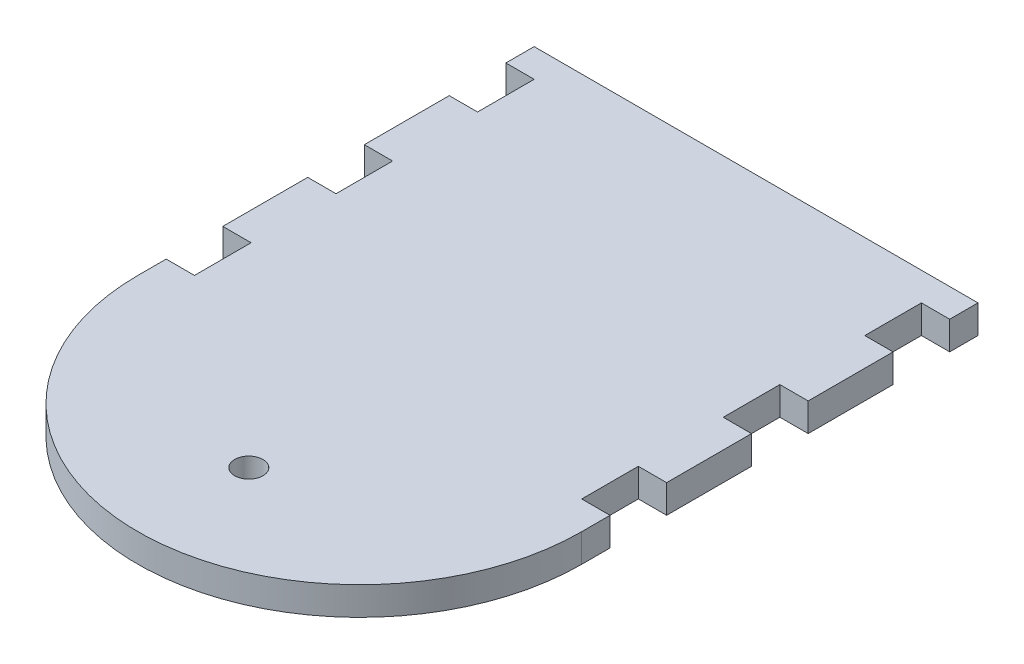
SolidWorks part; units mm, degrees
ref_plane "Front Plane" through (0, 0, 0) normal (0, 0, 1) x (1, 0, 0)
ref_plane "Top Plane" through (0, 0, 0) normal (0, 1, 0) x (1, 0, 0)
ref_plane "Right Plane" through (0, 0, 0) normal (1, 0, 0) x (0, 0, -1)
sketch "Sketch1" plane through (0, 0, 0) normal (0, 1, 0) x (1, 0, 0)
  line L0 (-49.784, 0) -> (49.784, 0) construction
  line L1 (-49.784, 44.45) -> (49.784, 44.45) construction
  line L2 (-49.784, 44.45) -> (-49.784, -44.45) construction
  line L3 (-49.784, -44.45) -> (49.784, -44.45) construction
  line L4 (49.784, 44.45) -> (49.784, -44.45) construction
  line L5 (-49.784, 44.45) -> (49.784, -44.45) construction
  line L6 (-49.784, -44.45) -> (49.784, 44.45) construction
  line L7 (-49.784, 44.45) -> (49.784, 44.45)
  line L8 (49.784, 44.45) -> (49.784, 38.1)
  line L9 (49.784, 38.1) -> (43.434, 38.1)
  line L10 (43.434, 38.1) -> (43.434, 25.4)
  line L11 (43.434, 25.4) -> (49.784, 25.4)
  line L12 (49.784, 25.4) -> (49.784, 6.35)
  line L13 (49.784, 6.35) -> (43.434, 6.35)
  line L14 (43.434, 6.35) -> (43.434, -6.35)
  line L15 (43.434, -6.35) -> (49.784, -6.35)
  line L16 (49.784, -6.35) -> (49.784, -25.4)
  line L17 (49.784, -25.4) -> (43.434, -25.4)
  line L18 (43.434, -25.4) -> (43.434, -38.1)
  line L19 (43.434, -38.1) -> (49.784, -38.1)
  line L20 (49.784, -38.1) -> (49.784, -44.45)
  line L21 (0, 44.45) -> (0, -44.45) construction
  line L22 (-43.434, -38.1) -> (-49.784, -38.1)
  line L23 (-43.434, -25.4) -> (-43.434, -38.1)
  line L24 (-49.784, -25.4) -> (-43.434, -25.4)
  line L25 (-43.434, -6.35) -> (-49.784, -6.35)
  line L26 (-43.434, 6.35) -> (-43.434, -6.35)
  line L27 (-49.784, 6.35) -> (-43.434, 6.35)
  line L28 (-43.434, 25.4) -> (-49.784, 25.4)
  line L29 (-43.434, 38.1) -> (-43.434, 25.4)
  line L30 (-49.784, 38.1) -> (-43.434, 38.1)
  line L31 (-49.784, 44.45) -> (-49.784, -44.45) construction
  line L32 (-49.784, -38.1) -> (-49.784, -44.45)
  line L33 (-49.784, -6.35) -> (-49.784, -25.4)
  line L34 (-49.784, 25.4) -> (-49.784, 6.35)
  line L35 (-49.784, 44.45) -> (-49.784, 38.1)
  line L36 (0, -44.45) -> (0, -94.234) construction
  arc A0 (-49.784, -44.45) -> (49.784, -44.45) centre (0, -44.45) ccw
  circle A1 centre (0, -69.342) radius 3.175
  point P0 (0, 0)
  point P9 (0, 0)
  dimension "D6" = 6.35
  dimension "D1" = 99.568
  dimension "D2" = 88.9
  dimension "D3" = 76.2
  dimension "D4" = 19.05
  dimension "D5" = 6.35
  dimension "D7" = 6.35
  dimension "D8" = 6.35
  dimension "D9" = 6.35
extrude "Boss-Extrude1" add sketch "Sketch1" along normal blind 6.35
